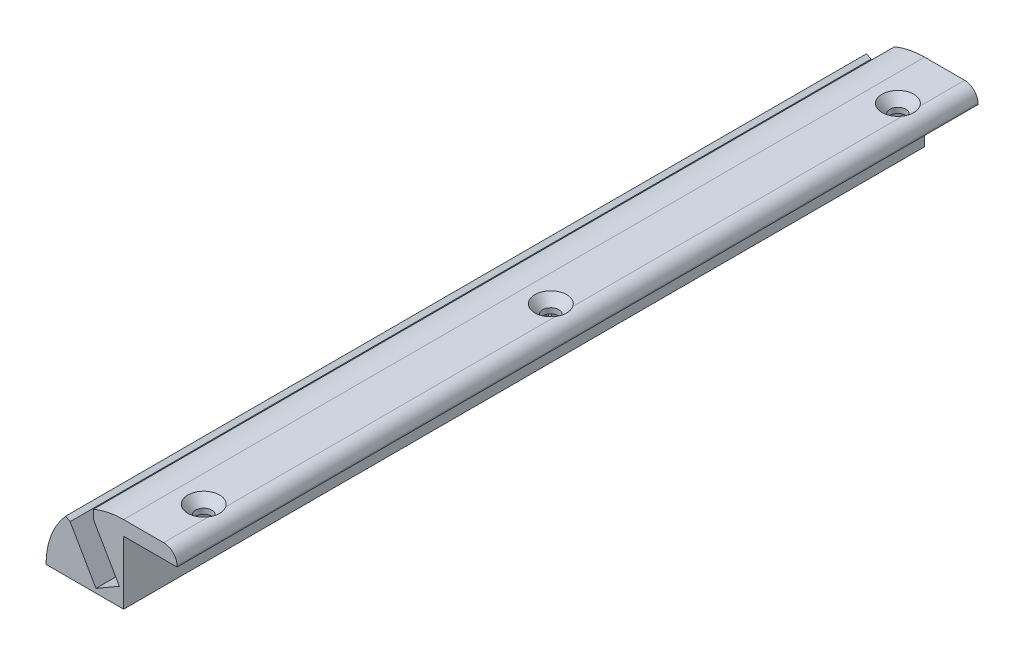
SolidWorks part; units mm, degrees
ref_plane "Front Plane" through (0, 0, 0) normal (0, 0, 1) x (1, 0, 0)
ref_plane "Top Plane" through (0, 0, 0) normal (0, 1, 0) x (1, 0, 0)
ref_plane "Right Plane" through (0, 0, 0) normal (1, 0, 0) x (0, 0, -1)
sketch "Sketch1" plane through (0, 0, 0) normal (0, 0, 1) x (1, 0, 0)
  line L0 (-43.8658, 7.3279) -> (-25.4, 7.3279)
  line L1 (-127, 7.3279) -> (127, 7.3279) construction
  line L2 (-25.4, 7.3279) -> (-25.4, 21.9837)
  line L3 (-25.4, 22.3647) -> (-14.6818, 22.3647)
  line L4 (-25.4, 21.9837) -> (228.6, 21.9837) construction
  line L5 (-25.4, 22.3647) -> (-25.4, 21.9837)
  line L6 (-38.1345, 19.0062) -> (-41.9445, 21.2059)
  line L7 (-41.9445, 21.2059) -> (-32.5693, 26.6187)
  line L8 (-32.5693, 26.6187) -> (-32.5693, 22.2193)
  line L9 (-25.4, 7.3279) -> (-34.6329, 23.3198) construction
  line L14 (-25.4, 25.7937) -> (-15.875, 25.7937)
  line L15 (-12.7, 22.6187) -> (-12.7, 22.3647)
  line L16 (-12.7, 22.3647) -> (-14.6818, 22.3647)
  line L18 (-38.1345, 19.0062) -> (-31.975, 8.3377)
  line L19 (-31.975, 8.3377) -> (-26.4098, 11.5508)
  line L20 (-26.4098, 11.5508) -> (-32.5693, 22.2193)
  line L21 (-32.5693, 22.2193) -> (-38.1345, 19.0062)
  line L22 (-38.1345, 19.0062) -> (-31.975, 8.3377)
  line L23 (-31.975, 8.3377) -> (-26.4098, 11.5508)
  line L24 (-26.4098, 11.5508) -> (-32.5693, 22.2193)
  line L25 (-32.5693, 22.2193) -> (-38.1345, 19.0062)
  arc A0 (-14.6818, 22.3647) -> (-43.8658, 7.3279) centre (-25.4, 7.3279) ccw
  arc A1 (-15.875, 25.7937) -> (-12.7, 22.6187) centre (-15.875, 22.6187) cw
  point P1 (0, 0)
  point P3 (-25.4, 25.7937)
  point P7 (-25.4, 21.9837)
  point P20 (-27.0497, 10.1852)
  point P25 (0, 0)
  point P27 (-37.132, 17.2699)
  point P28 (-31.3274, 20.0683)
  point P29 (0, 0)
  dimension "D8" = 3.175
  dimension "D1" = 3.81
  dimension "D2" = 0.381
  dimension "D3" = 60
  dimension "D4" = 0.1905
  dimension "D5" = 30
  dimension "D6" = 30
  dimension "D7" = 3.81
  dimension "D9" = 12.7
extrude "Boss-Extrude1" add sketch "Sketch1" along normal mid plane 190.5 contours L0 L9 L23 L22 L6 A0 | L9 L2 L5 L3 A0 L8 L24 L23 | A1 L14 A0 L16 L15
ref_plane "Plane1" through (0, 0, 82.55) normal (0, 0, 1) x (1, 0, 0)
sketch "Sketch4" plane through (0, 0, 82.55) normal (0, 0, 1) x (1, 0, 0)
  line L0 (-17.145, 22.3647) -> (-17.145, 23.6347)
  line L1 (-25.4, 22.3647) -> (-12.7, 22.3647) construction
  line L2 (-17.145, 23.6347) -> (-13.833, 27.4447)
  line L3 (-13.833, 27.4447) -> (-19.05, 27.4447)
  line L4 (-19.05, 27.4447) -> (-19.05, 22.3647)
  line L5 (-19.05, 22.3647) -> (-17.145, 22.3647)
  dimension "D1" = 1.905
  dimension "D2" = 1.27
  dimension "D3" = 41
  dimension "D4" = 5.08
  dimension "D5" = 6.35
revolve "Cut-Revolve1" cut sketch "Sketch4" angle 360 about L4
pattern_linear "LPattern1" count 3 spacing 82.55 along (0, 0, -1) of "Cut-Revolve1"
sketch "Sketch5" plane through (-25.4, 0, 0) normal (1, 0, 0) x (0, 0, -1)
  line L0 (-69.1647, 14.9479) -> (67.826, 14.9479) construction
  line L1 (-95.25, 7.3279) -> (95.25, 7.3279) construction
  text T0 "<b>Headboard Ceiling LED Mount V1</b>" font "Century Gothic" height 5.08
  point P3 (0, 14.9479)
  dimension "D1" = 7.62
extrude "Cut-Extrude2" cut sketch "Sketch5" against normal blind 0.635
